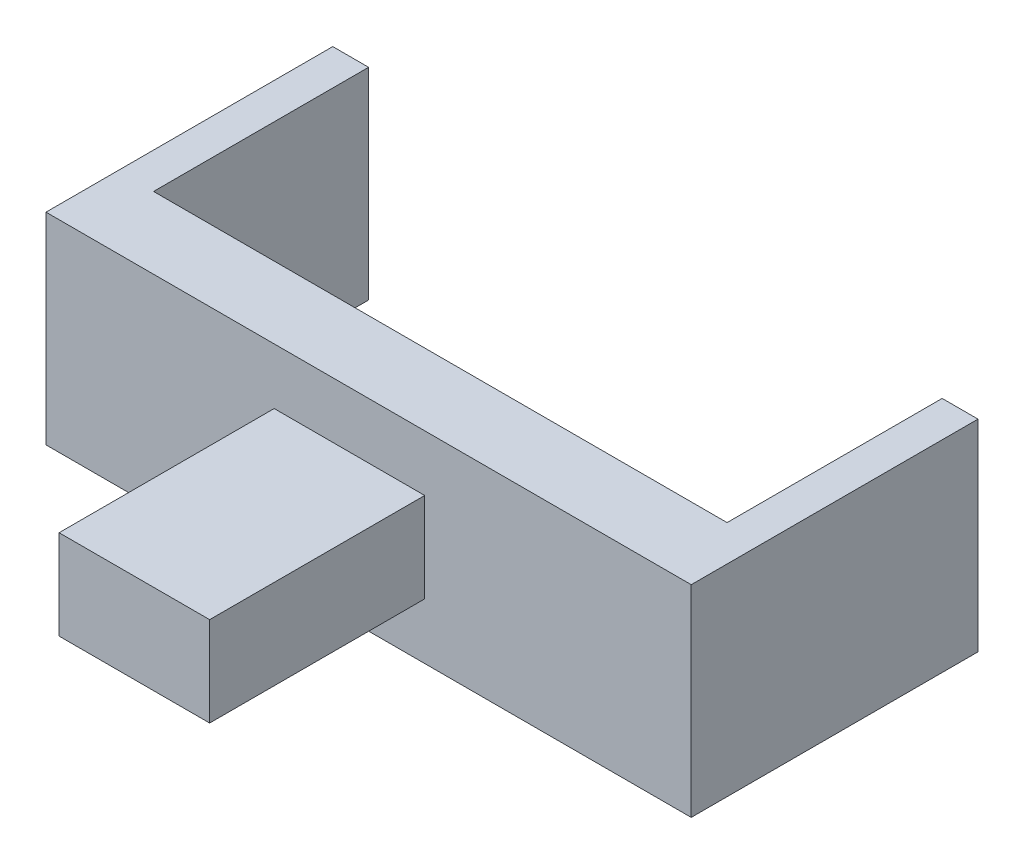
SolidWorks part; units mm, degrees
ref_plane "Front Plane" through (0, 0, 0) normal (0, 0, 1) x (1, 0, 0)
ref_plane "Top Plane" through (0, 0, 0) normal (0, 1, 0) x (1, 0, 0)
ref_plane "Right Plane" through (0, 0, 0) normal (1, 0, 0) x (0, 0, -1)
other "Configuration Table"
sketch "草图1" plane through (0, 0, 0) normal (0, 0, 1) x (1, 0, 0)
  line L1 (-42.3254, 17.5326) -> (47.6746, 17.5326)
  line L2 (-42.3254, 17.5326) -> (-42.3254, -10.5831)
  line L3 (-42.3254, -10.5831) -> (47.6746, -10.5831)
  line L4 (47.6746, 17.5326) -> (47.6746, -10.5831)
  dimension "D1" = 90
extrude "凸台-拉伸1" add sketch "草图1" along normal blind 10
sketch "草图2" plane through (0, 0, 10) normal (0, 0, 1) x (1, 0, 0)
  line L0 (-42.3254, 3.4748) -> (0, 3.4748) construction
  line L1 (-42.3254, 17.5326) -> (-42.3254, -10.5831) construction
  line L4 (-10.4996, -2.7714) -> (10.4996, -2.7714)
  line L5 (-10.4996, -2.7714) -> (-10.4996, 9.721)
  line L6 (-10.4996, 9.721) -> (10.4996, 9.721)
  line L7 (10.4996, -2.7714) -> (10.4996, 9.721)
  line L8 (-10.4996, -2.7714) -> (10.4996, 9.721) construction
  line L9 (-10.4996, 9.721) -> (10.4996, -2.7714) construction
extrude "凸台-拉伸2" add sketch "草图2" along normal blind 30
sketch "草图3" plane through (0, 0, 0) normal (0, 0, -1) x (-1, 0, 0)
  line L0 (-47.6746, 17.5326) -> (-42.6746, 17.5326)
  line L1 (-47.6746, 17.5326) -> (42.3254, 17.5326) construction
  line L2 (42.3254, -10.5831) -> (-47.6746, -10.5831) construction
  line L3 (-47.6746, 17.5326) -> (-42.6746, 17.5326)
  line L4 (-47.6746, 17.5326) -> (-47.6746, -10.5831)
  line L5 (-47.6746, -10.5831) -> (-42.6746, -10.5831)
  line L6 (-42.6746, 17.5326) -> (-42.6746, -10.5831)
  line L7 (-2.6746, 17.5326) -> (-2.6746, -10.5831) construction
  line L8 (37.3254, 17.5326) -> (37.3254, -10.5831)
  line L9 (42.3254, -10.5831) -> (37.3254, -10.5831)
  line L10 (42.3254, 17.5326) -> (42.3254, -10.5831)
  line L11 (42.3254, 17.5326) -> (37.3254, 17.5326)
  line L12 (42.3254, 17.5326) -> (37.3254, 17.5326)
  line M3 (42.3254, -10.5831) -> (42.3254, 17.5326)
  line M4 (42.3254, 17.5326) -> (-47.6746, 17.5326)
  line M5 (-47.6746, 17.5326) -> (-47.6746, -10.5831)
  line M6 (-47.6746, -10.5831) -> (42.3254, -10.5831)
  dimension "D1" = 5
extrude "凸台-拉伸3" add sketch "草图3" along normal blind 30 contours L8 M4 M6 M3 | L6 M4 M5 M6
